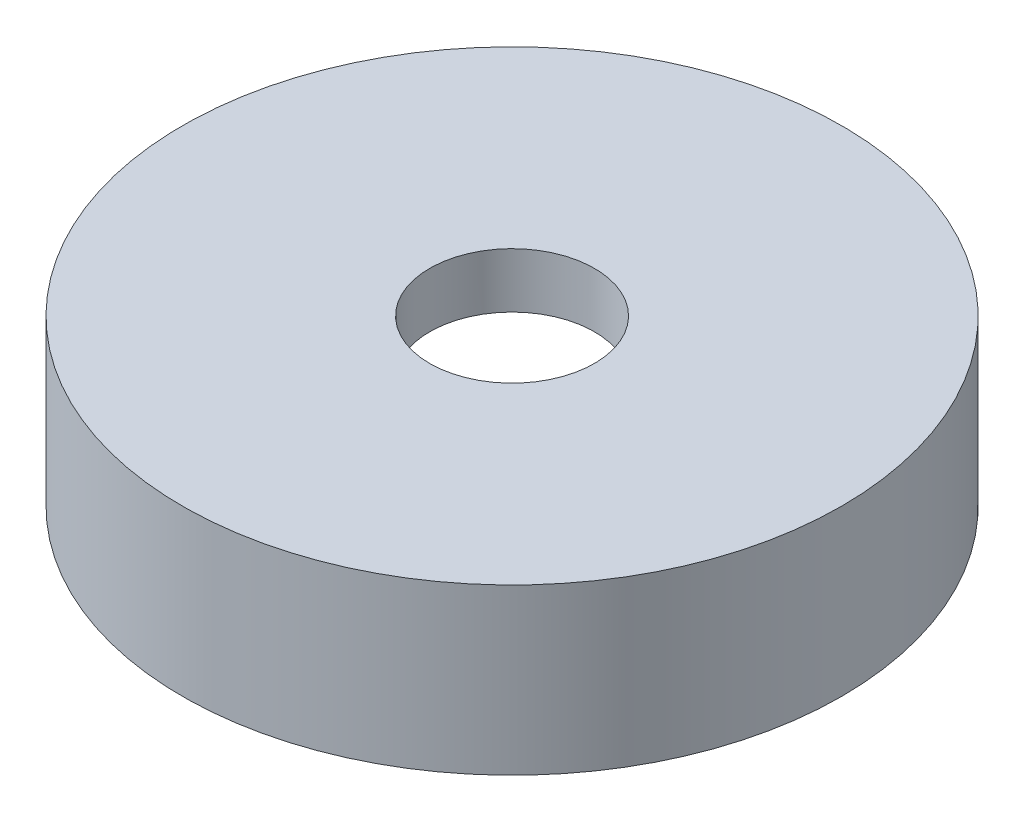
SolidWorks part; units mm, degrees
material "Alloy Steel (SS)"
ref_plane "Front Plane" through (0, 0, 0) normal (0, 0, 1) x (1, 0, 0)
ref_plane "Top Plane" through (0, 0, 0) normal (0, 1, 0) x (1, 0, 0)
ref_plane "Right Plane" through (0, 0, 0) normal (1, 0, 0) x (0, 0, -1)
sketch "Sketch1" plane through (0, 0, 0) normal (0, 0, 1) x (1, 0, 0)
  line L0 (0, 0) -> (0, 3) construction
  line L1 (0, 3) -> (6, 3)
  line L2 (6, 3) -> (6, 0)
  line L3 (0, 2) -> (5, 2)
  line L4 (5, 2) -> (5, 0)
  line L5 (0, 3) -> (0, 2)
  line L6 (5, 0) -> (6, 0)
  dimension "D1" = 6
  dimension "D2" = 3
  dimension "D3" = 1
revolve "Revolve1" add sketch "Sketch1" angle 360 about L0
hole_wizard "Ø3.0mm Dowel Hole1" positions "Sketch4" profile "Sketch5" hole size "Ø3.0" standard "ISO"
sketch "Sketch4" plane through (0, 3, 0) normal (0, 1, 0) x (1, 0, 0)
  point P0 (0, 0)
sketch "Sketch5" plane through (0, 3, 0) normal (1, 0, 0) x (0, 0, 1)
  line L0 (0, 0) -> (0, 8.5)
  line L1 (0, 8.5) -> (1.5, 7.5987)
  line L2 (1.5, 7.5987) -> (1.5, 0)
  line L5 (1.5, 0) -> (0, 0)
  line L10 (0, 8.5) -> (-1.5, 7.5987) construction
  line L11 (0, -6.35) -> (0, 107.95) construction
  dimension "Hole Dia." = 3
  dimension "Hole Depth" = 8.5
  dimension "Drill Angle" = 118
